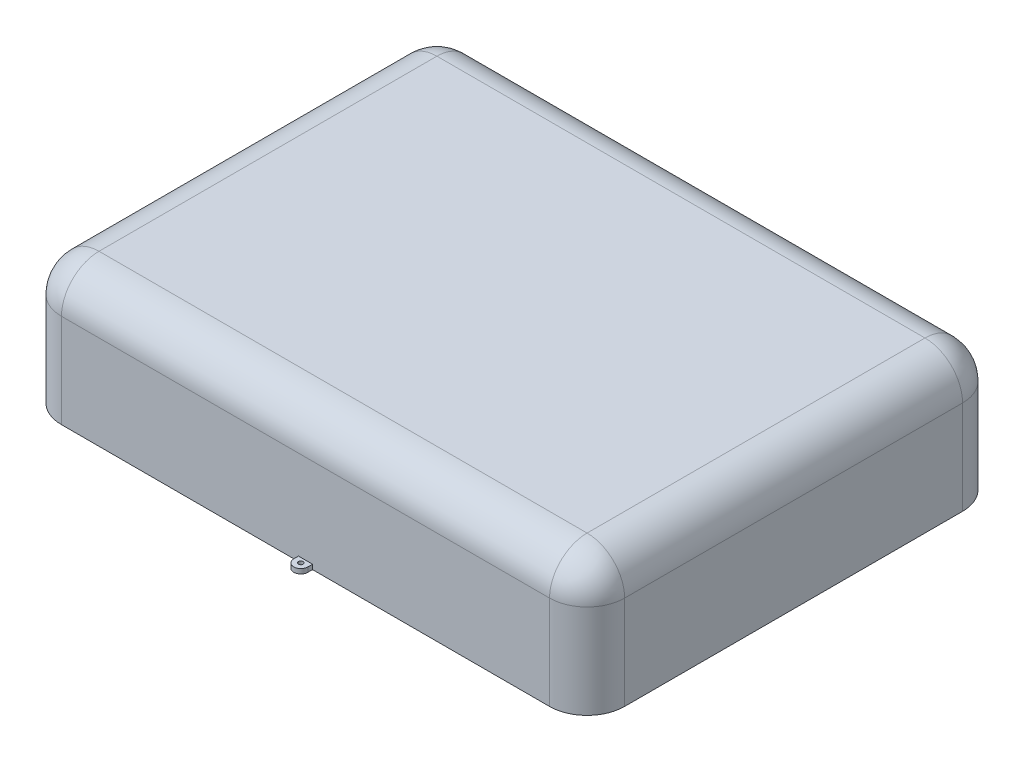
SolidWorks part; units mm, degrees
ref_plane "Front Plane" through (0, 0, 0) normal (0, 0, 1) x (1, 0, 0)
ref_plane "Top Plane" through (0, 0, 0) normal (0, 1, 0) x (1, 0, 0)
ref_plane "Right Plane" through (0, 0, 0) normal (1, 0, 0) x (0, 0, -1)
sketch "Sketch1" plane through (0, 0, 0) normal (0, 1, 0) x (1, 0, 0)
  line L0 (-2752.199, 0) -> (134857.7515, 0) construction
  line L1 (0, -2752.199) -> (0, 134857.7515) construction
  line L3 (381, -279.4) -> (-381, -279.4)
  line L4 (381, -279.4) -> (381, 279.4)
  line L5 (381, 279.4) -> (-381, 279.4)
  line L6 (-381, -279.4) -> (-381, 279.4)
  line L7 (381, -279.4) -> (-381, 279.4) construction
  line L8 (381, 279.4) -> (-381, -279.4) construction
  point P4 (0, 0)
  dimension "D1" = 558.8
  dimension "D2" = 762
extrude "Boss-Extrude1" add sketch "Sketch1" along normal blind 177.8
fillet "Fillet9" radius 50.8 8 edges at (0, 177.8, -279.4) (381, 177.8, 0) (0, 177.8, 279.4) (-381, 177.8, 0) (-381, 88.9, -279.4) (381, 88.9, -279.4) (381, 88.9, 279.4) (-381, 88.9, 279.4)
shell "Shell1" thickness 4.7625
sketch "Sketch3" plane through (0, 0, 0) normal (0, -1, 0) x (1, 0, 0)
  line L0 (330.2, 228.6) -> (330.2, 270.1562) construction
  line L1 (-330.2, 228.6) -> (-330.2, 479.9733) construction
  line L2 (-330.2, 279.4) -> (330.2, 279.4) construction
  line L3 (330.2, 279.4) -> (330.2, 284.1625)
  line L4 (330.2, 284.1625) -> (-330.2, 284.1625)
  line L5 (-330.2, 284.1625) -> (-330.2, 279.4)
  line L6 (-330.2, 279.4) -> (330.2, 279.4)
  dimension "D1" = 4.7625
sketch "Sketch4" plane through (0, 173.0375, 0) normal (0, -1, 0) x (1, 0, 0)
  line L0 (-1000, 0) -> (49000, 0) construction
  line L1 (0, -1000) -> (0, 49000) construction
  line L2 (190.5, 0) -> (190.5, -114.3) construction
  line L3 (0, 114.3) -> (190.5, 114.3) construction
  line L4 (-190.5, 114.3) -> (-190.5, 0) construction
  line L5 (-190.5, -114.3) -> (0, -114.3) construction
  line L6 (190.5, 114.3) -> (190.5, 0) construction
  line L7 (0, -114.3) -> (190.5, -114.3) construction
  line L8 (-190.5, 0) -> (-190.5, -114.3) construction
  line L9 (-190.5, 114.3) -> (0, 114.3) construction
  circle A1 centre (114.3, -68.58) radius 25.4 construction
  circle A3 centre (114.3, -68.58) radius 30.1625
  circle A4 centre (-114.3, -68.58) radius 25.4 construction
  circle A5 centre (-114.3, -68.58) radius 30.1625
  circle A6 centre (114.3, 68.58) radius 30.1625
  circle A7 centre (114.3, 68.58) radius 25.4 construction
  circle A8 centre (-114.3, 68.58) radius 25.4 construction
  circle A9 centre (-114.3, 68.58) radius 30.1625
  point P4 (0, 0)
  point P10 (114.3, -68.58)
  dimension "D5" = 4.7625
  dimension "D6" = 50.8
  dimension "D7" = 228.6
  dimension "D1" = 228.6
  dimension "D2" = 381
  dimension "D3" = 114.3
  dimension "D4" = 68.58
  dimension "D8" = 137.16
extrude "Boss-Extrude3" add sketch "Sketch4" along normal blind 77.7875
sketch "Sketch5" plane through (0, 95.25, 0) normal (0, -1, 0) x (1, 0, 0)
  line L0 (-1000, 0) -> (49000, 0) construction
  line L1 (0, -1000) -> (0, 49000) construction
  circle A0 centre (114.3, -68.58) radius 25.4
  circle A1 centre (114.3, -68.58) radius 19.685
  circle A2 centre (114.3, -68.58) radius 14.9225
  circle A3 centre (-114.3, -68.58) radius 14.9225
  circle A4 centre (-114.3, -68.58) radius 19.685
  circle A5 centre (-114.3, -68.58) radius 25.4
  circle A6 centre (114.3, 68.58) radius 14.9225
  circle A7 centre (114.3, 68.58) radius 19.685
  circle A8 centre (114.3, 68.58) radius 25.4
  circle A9 centre (-114.3, 68.58) radius 14.9225
  circle A10 centre (-114.3, 68.58) radius 19.685
  circle A11 centre (-114.3, 68.58) radius 25.4
  dimension "D1" = 50.8
  dimension "D2" = 39.37
  dimension "D3" = 4.7625
extrude "Cut-Extrude1" cut sketch "Sketch5" against normal blind 12.7 contours A0 A1 | A2 | A5 A4 | A3 | A8 A7 | A6 | A11 A10 | A9
fillet "Fillet13" radius 2.54 4 edges at (-114.3, 173.0375, 98.7425) (114.3, 173.0375, 98.7425) (-114.3, 173.0375, -38.4175) (114.3, 173.0375, -38.4175)
sketch "Sketch6" plane through (0, 0, 0) normal (1, 0, 0) x (0, 0, -1)
  line L0 (-1000, 0) -> (279.4, 0) construction
  line L1 (279.4, 0) -> (279.4, 127) construction
  line L2 (282.575, 0) -> (288.925, 0) construction
  line L3 (282.575, 0) -> (279.4, 0) construction
  line L4 (288.925, 9.525) -> (288.925, 30.48)
  line L5 (288.925, 30.48) -> (279.4, 30.48)
  line L6 (279.4, 0) -> (279.4, 30.48)
  line L7 (288.925, 0) -> (49000, 0) construction
  line L8 (288.925, 0) -> (282.575, 0) construction
  line L9 (288.925, 0) -> (288.925, 6.35) construction
  line L10 (288.925, 6.35) -> (288.925, 9.525) construction
  line L11 (279.4, 0) -> (282.575, 0) construction
  arc A0 (279.4, 0) -> (288.925, 9.525) centre (288.925, 0) ccw
  circle A1 centre (288.925, 0) radius 6.35
  arc A2 (288.925, 9.525) -> (279.4, 0) centre (288.925, 0) ccw construction
  dimension "D1" = 19.05
  dimension "D2" = 12.7
  dimension "D3" = 30.48
extrude "Boss-Extrude4" add sketch "Sketch6" along normal blind 273.05 and the other way blind 273.05
sketch "Sketch7" plane through (0, 177.8, 0) normal (0, 1, 0) x (1, 0, 0)
  line L0 (-330.2, 279.4) -> (330.2, 279.4) construction
  line L1 (0, -1000) -> (0, 49000) construction
  line L2 (273.05, 298.45) -> (-273.05, 298.45) construction
  line L3 (-133.35, 279.4) -> (133.35, 279.4)
  line L4 (0, 279.4) -> (0, 298.45)
  line L5 (-133.35, 298.45) -> (133.35, 298.45)
  line L6 (133.35, 279.4) -> (133.35, 298.45)
  line L7 (-133.35, 279.4) -> (-133.35, 298.45)
  line L8 (273.05, 279.4) -> (273.05, 298.45) construction
  line L9 (146.05, 279.4) -> (158.75, 279.4)
  line L10 (146.05, 279.4) -> (146.05, 298.45)
  line L11 (146.05, 298.45) -> (158.75, 298.45)
  line L12 (158.75, 279.4) -> (158.75, 298.45)
  line L13 (171.45, 279.4) -> (184.15, 279.4)
  line L14 (171.45, 279.4) -> (171.45, 298.45)
  line L15 (171.45, 298.45) -> (184.15, 298.45)
  line L16 (184.15, 279.4) -> (184.15, 298.45)
  line L17 (196.85, 279.4) -> (209.55, 279.4)
  line L18 (196.85, 279.4) -> (196.85, 298.45)
  line L19 (196.85, 298.45) -> (209.55, 298.45)
  line L20 (209.55, 279.4) -> (209.55, 298.45)
  line L21 (222.25, 279.4) -> (234.95, 279.4)
  line L22 (222.25, 279.4) -> (222.25, 298.45)
  line L23 (222.25, 298.45) -> (234.95, 298.45)
  line L24 (234.95, 279.4) -> (234.95, 298.45)
  line L25 (247.65, 279.4) -> (260.35, 279.4)
  line L26 (247.65, 279.4) -> (247.65, 298.45)
  line L27 (247.65, 298.45) -> (260.35, 298.45)
  line L28 (260.35, 279.4) -> (260.35, 298.45)
  line L29 (-247.65, 298.45) -> (-260.35, 298.45)
  line L30 (-260.35, 279.4) -> (-260.35, 298.45)
  line L31 (-247.65, 279.4) -> (-260.35, 279.4)
  line L32 (-247.65, 279.4) -> (-247.65, 298.45)
  line L33 (-222.25, 298.45) -> (-234.95, 298.45)
  line L34 (-234.95, 279.4) -> (-234.95, 298.45)
  line L35 (-222.25, 279.4) -> (-234.95, 279.4)
  line L36 (-222.25, 279.4) -> (-222.25, 298.45)
  line L37 (-196.85, 298.45) -> (-209.55, 298.45)
  line L38 (-209.55, 279.4) -> (-209.55, 298.45)
  line L39 (-196.85, 279.4) -> (-209.55, 279.4)
  line L40 (-196.85, 279.4) -> (-196.85, 298.45)
  line L41 (-171.45, 298.45) -> (-184.15, 298.45)
  line L42 (-184.15, 279.4) -> (-184.15, 298.45)
  line L43 (-171.45, 279.4) -> (-184.15, 279.4)
  line L44 (-171.45, 279.4) -> (-171.45, 298.45)
  line L45 (-146.05, 298.45) -> (-158.75, 298.45)
  line L46 (-158.75, 279.4) -> (-158.75, 298.45)
  line L47 (-146.05, 279.4) -> (-158.75, 279.4)
  line L48 (-146.05, 279.4) -> (-146.05, 298.45)
  dimension "D1" = 133.35
  dimension "D2" = 12.7
  dimension "D3" = 12.7
  dimension "D4" = 12.7
  dimension "D5" = 12.7
  dimension "D6" = 12.7
  dimension "D7" = 12.7
  dimension "D8" = 12.7
  dimension "D9" = 12.7
  dimension "D10" = 12.7
  dimension "D11" = 12.7
  dimension "D12" = 12.7
extrude "Cut-Extrude2" cut sketch "Sketch7" against normal blind 203.2 contours L3 L6 L5 L4 | L7 L3 L4 L5 | L47 L48 L45 L46 | L43 L44 L41 L42 | L39 L40 L37 L38 | L35 L36 L33 L34 | L31 L32 L29 L30 | L9 L12 L11 L10 | L13 L16 L15 L14 | L17 L20 L19 L18 | L21 L24 L23 L22 | L25 L28 L27 L26
sketch "Sketch8" plane through (-273.05, 0, 0) normal (-1, 0, 0) x (0, 0, 1)
  line L0 (-279.4, 0) -> (-279.4, 55.3186) construction
  line L1 (-279.4, 0) -> (-279.4, 127) construction
  line L2 (-288.925, 30.48) -> (-279.4, 30.48) construction
  line L3 (-288.925, 0) -> (-288.925, 30.48) construction
  line L4 (-282.575, 0) -> (-279.4, 0) construction
  line L5 (-282.575, 0) -> (-282.575, 30.48) construction
  line L6 (-288.925, 9.525) -> (-288.925, 30.48)
  line L7 (-288.925, 30.48) -> (-282.575, 30.48)
  line L8 (-282.575, 30.48) -> (-282.575, 7.0995)
  line L9 (-295.275, 0) -> (-298.45, 0)
  line L10 (-282.575, 0) -> (-279.4, 0)
  circle A0 centre (-288.925, 0) radius 6.35 construction
  arc A1 (-298.45, 0) -> (-279.4, 0) centre (-288.925, 0) ccw
  arc A2 (-295.275, 0) -> (-282.575, 0) centre (-288.925, 0) ccw
  arc A3 (-282.575, 7.0995) -> (-288.925, 9.525) centre (-288.925, 0) ccw
extrude "Cut-Extrude3" cut sketch "Sketch8" against normal blind 12.7
pattern_linear "LPattern1" count 3 spacing 50.8 along (1, 0, 0) of "Cut-Extrude3"
mirror "Mirror1" about plane through (0, 0, 0) normal (1, 0, 0) of "Cut-Extrude3", "LPattern1"
sketch "Sketch10" plane through (-247.65, 0, 0) normal (-1, 0, 0) x (0, 0, 1)
  line L0 (-298.45, 0) -> (-295.275, 0)
  line L1 (-282.575, 0) -> (-282.575, 30.48)
  line L2 (-282.575, 30.48) -> (-288.925, 30.48)
  line L3 (-288.925, 30.48) -> (-288.925, 9.525)
  line L4 (-298.45, 0) -> (-282.575, 0) construction
  arc A0 (-282.575, 0) -> (-295.275, 0) centre (-288.925, 0) ccw
  arc A1 (-288.925, 9.525) -> (-298.45, 0) centre (-288.925, 0) ccw
extrude "Cut-Extrude4" cut sketch "Sketch10" against normal blind 12.7
pattern_linear "LPattern2" count 3 spacing 50.8 along (1, 0, 0) of "Cut-Extrude4"
mirror "Mirror2" about plane through (0, 0, 0) normal (1, 0, 0) of "Cut-Extrude4", "LPattern2"
fillet "Fillet14" radius 2.54 12 edges at (-241.3, 0, -279.4) (-190.5, 0, -279.4) (-139.7, 0, -279.4) (139.7, 0, -279.4) (190.5, 0, -279.4) (241.3, 0, -279.4) (-266.7, 7.0995, -282.575) (-215.9, 7.0995, -282.575) (-165.1, 7.0995, -282.575) (266.7, 7.0995, -282.575) (215.9, 7.0995, -282.575) (165.1, 7.0995, -282.575)
sketch "Sketch11" plane through (0, 107.95, 0) normal (0, -1, 0) x (1, 0, 0)
  line L0 (-1000, 0) -> (49000, 0) construction
  line L1 (0, -1000) -> (0, 49000) construction
  circle A0 centre (-114.3, 68.58) radius 14.9225
  circle A1 centre (-114.3, -68.58) radius 14.9225
  circle A2 centre (114.3, -68.58) radius 14.9225
  circle A3 centre (114.3, 68.58) radius 14.9225
extrude "Cut-Extrude5" cut sketch "Sketch11" against normal blind 65.0875
sketch "Sketch12" plane through (0, 0, 0) normal (1, 0, 0) x (0, 0, -1)
  line L0 (228.6, 177.8) -> (228.6, 127) construction
  line L1 (228.6, 127) -> (279.4, 127) construction
  line L2 (228.6, 173.0375) -> (274.6375, 109.5375)
  line L3 (274.6375, 127) -> (274.6375, 0) construction
  line L4 (274.6375, 127) -> (274.6375, 109.5375)
  arc A0 (228.6, 173.0375) -> (274.6375, 127) centre (228.6, 127) cw
  arc A1 (274.6375, 127) -> (228.6, 173.0375) centre (228.6, 127) ccw construction
  dimension "D1" = 63.5
extrude "Boss-Extrude5" add sketch "Sketch12" along normal mid plane 2.54
pattern_linear "LPattern3" count 8 spacing 43.18 along (1, 0, 0) count 8 spacing 43.18 along (-1, 0, 0) of "Boss-Extrude5"
mirror "Mirror3" about plane through (0, 0, 0) normal (0, 0, 1) of "Boss-Extrude5", "LPattern3"
sketch "Sketch13" plane through (0, 0, 0) normal (0, 0, 1) x (1, 0, 0)
  line L0 (330.2, 127) -> (381, 127) construction
  line L1 (330.2, 173.0375) -> (376.2375, 109.5375)
  line L2 (376.2375, 127) -> (376.2375, 0) construction
  line L3 (376.2375, 127) -> (376.2375, 109.5375)
  arc A0 (330.2, 173.0375) -> (376.2375, 127) centre (330.2, 127) cw
  dimension "D1" = 63.5
extrude "Boss-Extrude6" add sketch "Sketch13" along normal mid plane 2.54
pattern_linear "LPattern4" count 5 spacing 44.45 along (0, 0, 1) count 5 spacing 44.45 along (0, 0, -1) of "Boss-Extrude6"
mirror "Mirror4" about plane through (0, 0, 0) normal (1, 0, 0) of "Boss-Extrude6", "LPattern4"
sketch "Sketch14" plane through (0, 0, 0) normal (0, 1, 0) x (1, 0, 0)
  line L0 (-1000, 0) -> (49000, 0) construction
  line L1 (0, -1000) -> (0, -276.225) construction
  line L2 (-330.2, -279.4) -> (-7.3388, -279.4) construction
  line L4 (0, -279.4) -> (0, -276.225) construction
  line L5 (0, -276.225) -> (0, 49000) construction
  line L6 (0, -279.4) -> (-0.9888, -279.4) construction
  line L7 (-0.9888, -279.4) -> (330.2, -279.4) construction
  line L8 (0, -279.4) -> (-0.9888, -279.4) construction
  line L10 (-7.3388, -279.4) -> (0, -279.4) construction
  line L11 (-7.3388, -279.4) -> (0, -279.4) construction
  line L12 (0, -276.225) -> (0, -279.4) construction
  line L13 (0, -285.75) -> (-9.525, -285.75) construction
  line L14 (9.525, -285.75) -> (9.525, -279.4)
  line L16 (-9.525, -285.75) -> (-9.525, -279.4)
  line L21 (9.525, -285.75) -> (0, -285.75) construction
  line L22 (-9.525, -279.4) -> (9.525, -279.4)
  arc A0 (330.2, -279.4) -> (381, -228.6) centre (330.2, -228.6) ccw construction
  arc A1 (-9.525, -285.75) -> (9.525, -285.75) centre (0, -285.75) ccw
  arc A5 (-9.525, -285.75) -> (9.525, -285.75) centre (0, -285.75) ccw construction
  circle A6 centre (0, -285.75) radius 3.175
  arc A7 (-9.525, -285.75) -> (9.525, -285.75) centre (0, -285.75) ccw construction
  dimension "D1" = 6.35
  dimension "D2" = 19.05
  dimension "D3" = 6.35
extrude "Boss-Extrude7" add sketch "Sketch14" along normal blind 6.35
